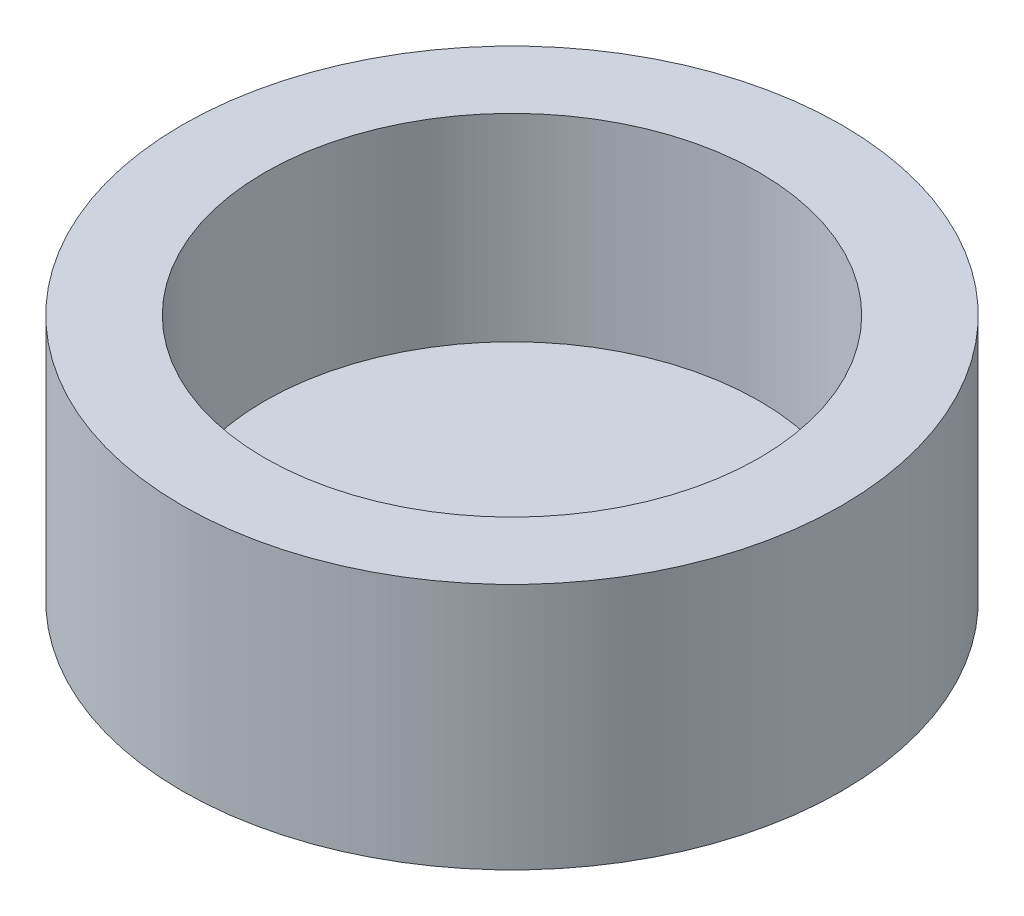
SolidWorks part; units mm, degrees
ref_plane "Front Plane" through (0, 0, 0) normal (0, 0, 1) x (1, 0, 0)
ref_plane "Top Plane" through (0, 0, 0) normal (0, 1, 0) x (1, 0, 0)
ref_plane "Right Plane" through (0, 0, 0) normal (1, 0, 0) x (0, 0, -1)
sketch "Sketch1" plane through (0, 0, 0) normal (0, 1, 0) x (1, 0, 0)
  circle A0 centre (0, 0) radius 25.4
extrude "Boss-Extrude1" add sketch "Sketch1" along normal blind 19.05
sketch "Sketch2" plane through (0, 19.05, 0) normal (0, 1, 0) x (1, 0, 0)
  circle A0 centre (0, 0) radius 19.05
extrude "Cut-Extrude1" cut sketch "Sketch2" against normal offset from surface (15.24 mm away) 3.81 up to face at (0, 0, 25.4)
